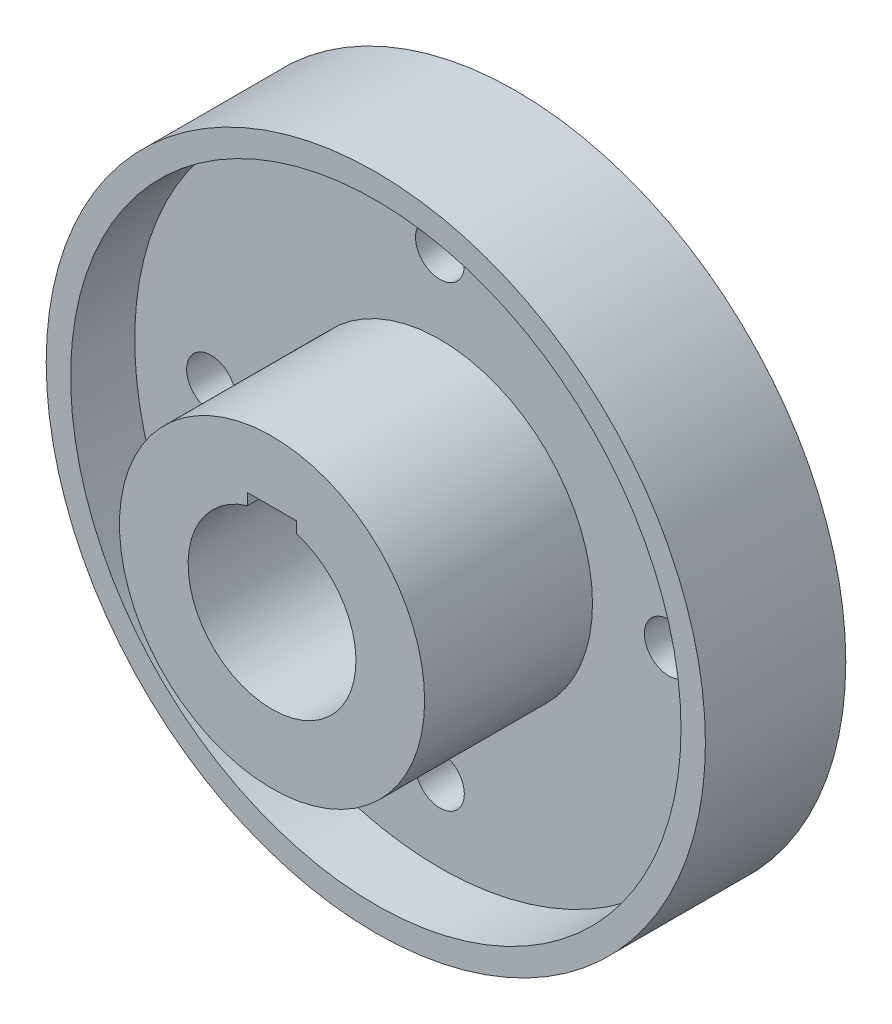
SolidWorks part; units mm, degrees
material "Gray Cast Iron"
ref_plane "Front Plane" through (0, 0, 0) normal (0, 0, 1) x (1, 0, 0)
ref_plane "Top Plane" through (0, 0, 0) normal (0, 1, 0) x (1, 0, 0)
ref_plane "Right Plane" through (0, 0, 0) normal (1, 0, 0) x (0, 0, -1)
sketch "Sketch1" plane through (0, 0, 0) normal (0, 0, 1) x (1, 0, 0)
  circle A0 centre (0, 0) radius 108
  dimension "D1" = 216
extrude "Boss-Extrude1" add sketch "Sketch1" along normal blind 25
sketch "Sketch2" plane through (0, 0, 25) normal (0, 0, 1) x (1, 0, 0)
  circle A0 centre (0, 0) radius 108
  circle A1 centre (0, 0) radius 100
  dimension "D1" = 216
  dimension "D2" = 200
extrude "Boss-Extrude2" add sketch "Sketch2" along normal blind 21
sketch "Sketch3" plane through (0, 0, 25) normal (0, 0, 1) x (1, 0, 0)
  circle A0 centre (0, 0) radius 50
  circle A1 centre (0, 0) radius 27.5
  dimension "D1" = 100
  dimension "D2" = 55
extrude "Boss-Extrude3" add sketch "Sketch3" along normal blind 55
sketch "Sketch4" plane through (0, 0, 25) normal (0, 0, 1) x (1, 0, 0)
  line L0 (0, 0) -> (0, 75) construction
  circle A0 centre (0, 0) radius 75 construction
  circle A1 centre (0, 75) radius 8
  circle A2 centre (75, 0) radius 8
  circle A3 centre (0, -75) radius 8
  circle A4 centre (-75, 0) radius 8
  circle A5 centre (0, 0) radius 50 construction
  point P14 (0, 0)
  dimension "D1" = 150
  dimension "D2" = 16
  dimension "D4" = 75
  dimension "D5" = 75
  dimension "D3" = 4
extrude "Cut-Extrude1" cut sketch "Sketch4" against normal through all
sketch "Sketch5" plane through (0, 0, 0) normal (0, 0, -1) x (-1, 0, 0)
  circle A0 centre (0, 0) radius 37.5
  dimension "D1" = 75
extrude "Cut-Extrude2" cut sketch "Sketch5" against normal blind 6
sketch "Sketch6" plane through (0, 0, 25) normal (0, 0, 1) x (1, 0, 0)
  circle A1 centre (0, 0) radius 27.5
  dimension "D2" = 55
extrude "Cut-Extrude4" cut sketch "Sketch6" against normal through all contours A1
sketch "Sketch7" plane through (0, 0, 80) normal (0, 0, 1) x (1, 0, 0)
  line L0 (0, 30) -> (0, 0) construction
  line L1 (-8, 30) -> (8, 30)
  line L2 (-8, 30) -> (-8, 0)
  line L3 (-8, 0) -> (8, 0)
  line L4 (8, 0) -> (8, 30)
  circle A1 centre (0, 0) radius 50 construction
  point P7 (0, 30)
  dimension "D1" = 30
  dimension "D2" = 16
extrude "Cut-Extrude5" cut sketch "Sketch7" against normal through all
